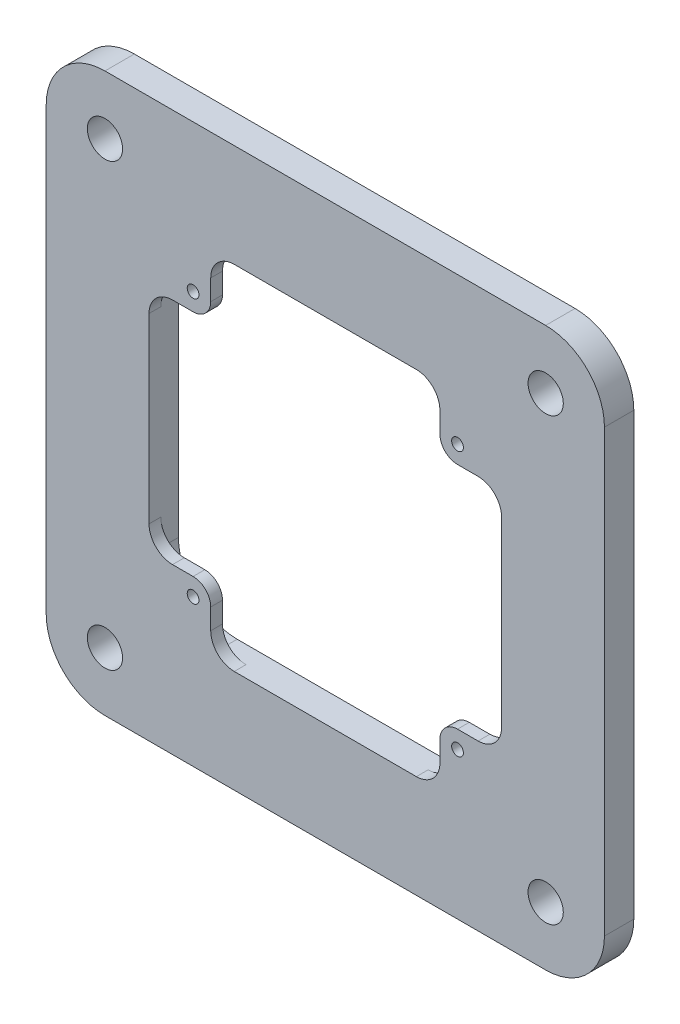
SolidWorks part; units mm, degrees
ref_plane "前视基准面" through (0, 0, 0) normal (0, 0, 1) x (1, 0, 0)
ref_plane "上视基准面" through (0, 0, 0) normal (0, 1, 0) x (1, 0, 0)
ref_plane "右视基准面" through (0, 0, 0) normal (1, 0, 0) x (0, 0, -1)
sketch "草图1" plane through (0, 0, 0) normal (0, 0, 1) x (1, 0, 0)
  line L0 (-47.5, 37.5) -> (-47.5, -37.5) construction
  line L1 (-37.5, 47.5) -> (37.5, 47.5)
  line L2 (-47.5, 37.5) -> (-47.5, -37.5)
  line L3 (-37.5, -47.5) -> (37.5, -47.5)
  line L4 (47.5, 37.5) -> (47.5, -37.5)
  line L5 (-47.5, 47.5) -> (47.5, -47.5) construction
  line L6 (-47.5, -47.5) -> (47.5, 47.5) construction
  line L7 (0, 0) -> (0, 59.9603) construction
  line L8 (-22.5, 22.5) -> (22.5, 22.5) construction
  line L9 (-22.5, 22.5) -> (-22.5, -22.5) construction
  line L10 (-22.5, -22.5) -> (22.5, -22.5) construction
  line L11 (22.5, 22.5) -> (22.5, -22.5) construction
  line L12 (-22.5, 22.5) -> (22.5, -22.5) construction
  line L13 (-22.5, -22.5) -> (22.5, 22.5) construction
  line L14 (-17.8068, 0) -> (11.5296, 0) construction
  line L15 (15.5, 30) -> (-15.5, 30)
  line L16 (25, 30) -> (-25, 30) construction
  line L17 (-19.5, 26) -> (-19.5, 22.5)
  line L18 (-22.5, 19.5) -> (-26, 19.5)
  line L19 (-30, 25) -> (-30, 14) construction
  line L20 (-30, 15.5) -> (-30, -15.5)
  line L21 (30, 15.5) -> (30, -15.5)
  line L22 (22.5, 19.5) -> (26, 19.5)
  line L23 (19.5, 26) -> (19.5, 22.5)
  line L24 (22.5, -19.5) -> (26, -19.5)
  line L25 (19.5, -26) -> (19.5, -22.5)
  line L26 (15.5, -30) -> (-15.5, -30)
  line L27 (-19.5, -26) -> (-19.5, -22.5)
  line L28 (-22.5, -19.5) -> (-26, -19.5)
  arc A0 (-47.5, -37.5) -> (-37.5, -47.5) centre (-37.5, -37.5) ccw
  arc A1 (37.5, -47.5) -> (47.5, -37.5) centre (37.5, -37.5) ccw
  arc A2 (37.5, 47.5) -> (47.5, 37.5) centre (37.5, 37.5) cw
  arc A3 (-37.5, 47.5) -> (-47.5, 37.5) centre (-37.5, 37.5) ccw
  circle A4 centre (-22.5, 22.5) radius 1
  circle A5 centre (22.5, 22.5) radius 1
  circle A6 centre (22.5, -22.5) radius 1
  circle A7 centre (-22.5, -22.5) radius 1
  circle A8 centre (37.5, 37.5) radius 3
  circle A9 centre (-37.5, 37.5) radius 3
  circle A10 centre (-37.5, -37.5) radius 3
  circle A11 centre (37.5, -37.5) radius 3
  arc A12 (-19.5, 22.5) -> (-22.5, 19.5) centre (-22.5, 22.5) cw
  arc A13 (-26, 19.5) -> (-30, 15.5) centre (-26, 15.5) ccw
  arc A14 (-15.5, 30) -> (-19.5, 26) centre (-15.5, 26) ccw
  arc A15 (26, 19.5) -> (30, 15.5) centre (26, 15.5) cw
  arc A16 (19.5, 22.5) -> (22.5, 19.5) centre (22.5, 22.5) ccw
  arc A17 (15.5, 30) -> (19.5, 26) centre (15.5, 26) cw
  arc A18 (26, -19.5) -> (30, -15.5) centre (26, -15.5) ccw
  arc A19 (19.5, -22.5) -> (22.5, -19.5) centre (22.5, -22.5) cw
  arc A20 (15.5, -30) -> (19.5, -26) centre (15.5, -26) ccw
  arc A21 (-15.5, -30) -> (-19.5, -26) centre (-15.5, -26) cw
  arc A22 (-19.5, -22.5) -> (-22.5, -19.5) centre (-22.5, -22.5) ccw
  arc A23 (-26, -19.5) -> (-30, -15.5) centre (-26, -15.5) cw
  point P0 (0, 0)
  point P20 (0, 0)
  point P38 (-100.2195, 50.7564)
  point P44 (-84.5603, 35.197)
  point P50 (-19.5, 19.5)
  point P53 (-30, 19.5)
  point P56 (-19.5, 30)
  point P66 (0, 30)
  point P67 (30, 0)
  point P82 (-30, 0)
  dimension "D1" = 10
  dimension "D2" = 2
  dimension "D4" = 6
  dimension "D6" = 3
  dimension "D7" = 4
  dimension "D3" = 45
extrude "凸台-拉伸1" add sketch "草图1" along normal blind 5
sketch "草图2" plane through (0, 0, 0) normal (0, 0, -1) x (-1, 0, 0)
  line L0 (-25, 30) -> (25, 30) construction
  line L1 (20, -30) -> (-20, -30)
  line L2 (30, -20) -> (30, 20)
  line L3 (20, 30) -> (-20, 30)
  line L4 (-30, -20) -> (-30, 20)
  line L5 (30, -30) -> (-30, 30) construction
  line L6 (30, 30) -> (-30, -30) construction
  arc A0 (20, -30) -> (30, -20) centre (20, -20) ccw
  arc A1 (-20, -30) -> (-30, -20) centre (-20, -20) cw
  arc A2 (-20, 30) -> (-30, 20) centre (-20, 20) ccw
  arc A3 (30, 20) -> (20, 30) centre (20, 20) ccw
  point P0 (0, 0)
  dimension "D1" = 10
  dimension "D2" = 10
extrude "切除-拉伸1" cut sketch "草图2" against normal blind 3
